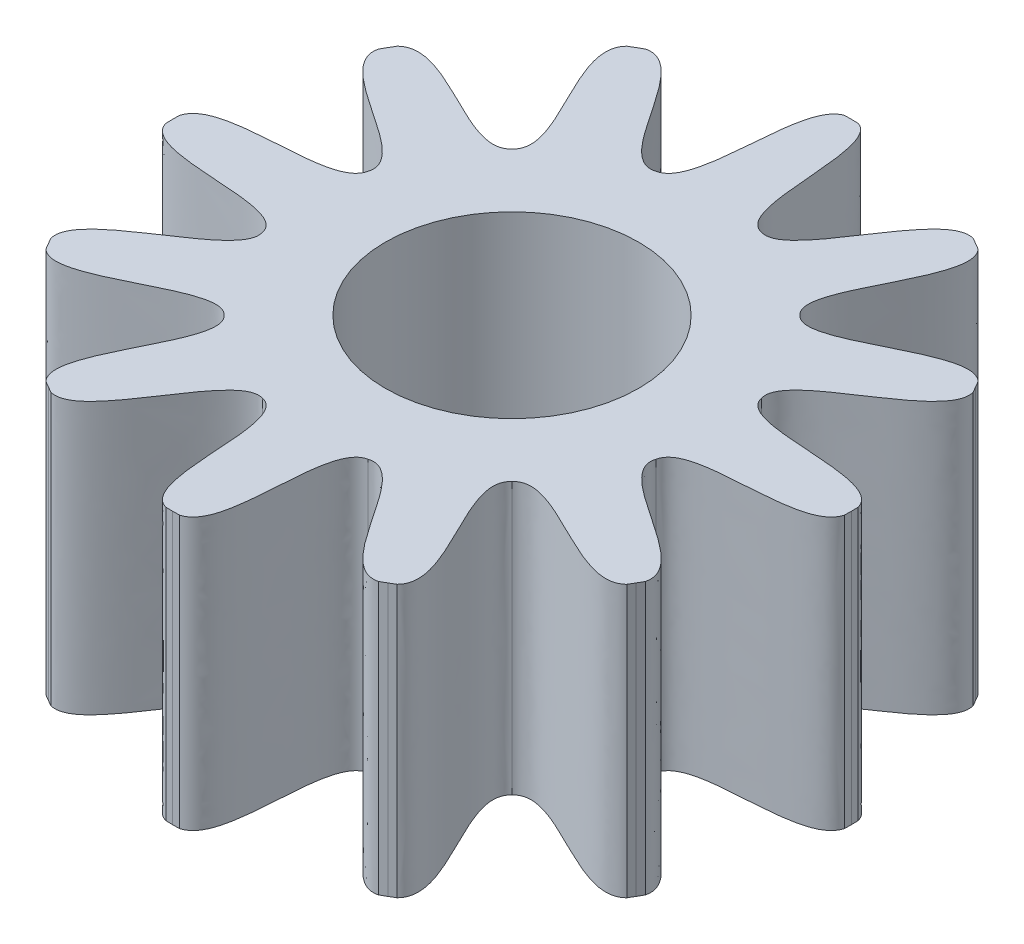
SolidWorks part; units mm, degrees
ref_plane "Alzado" through (0, 0, 0) normal (0, 0, 1) x (1, 0, 0)
ref_plane "Planta" through (0, 0, 0) normal (0, 1, 0) x (1, 0, 0)
ref_plane "Vista lateral" through (0, 0, 0) normal (1, 0, 0) x (0, 0, -1)
sketch "Sketch1" plane through (0, 0, 0) normal (0, 1, 0) x (1, 0, 0)
  line L0 (0, -1000) -> (0, 49000) construction
  line L1 (0, 0) -> (12940.9523, 48296.2913) construction
  line L2 (0, 0.75) -> (0.015, 0.7499)
  line L3 (0, 0.75) -> (-0.015, 0.7499)
  line L4 (0.375, 0.6495) -> (0.3619, 0.6569)
  line L5 (0.375, 0.6495) -> (0.3879, 0.6419)
  line L6 (0.6495, 0.375) -> (0.6419, 0.3879)
  line L7 (0.6495, 0.375) -> (0.6569, 0.3619)
  line L8 (0.75, 0) -> (0.7499, 0.015)
  line L9 (0.75, 0) -> (0.7499, -0.015)
  line L10 (0.6495, -0.375) -> (0.6569, -0.3619)
  line L11 (0.6495, -0.375) -> (0.6419, -0.3879)
  line L12 (0.375, -0.6495) -> (0.3879, -0.6419)
  line L13 (0.375, -0.6495) -> (0.3619, -0.6569)
  line L14 (0, -0.75) -> (0.015, -0.7499)
  line L15 (0, -0.75) -> (-0.015, -0.7499)
  line L16 (-0.375, -0.6495) -> (-0.3619, -0.6569)
  line L17 (-0.375, -0.6495) -> (-0.3879, -0.6419)
  line L18 (-0.6495, -0.375) -> (-0.6419, -0.3879)
  line L19 (-0.6495, -0.375) -> (-0.6569, -0.3619)
  line L20 (-0.75, 0) -> (-0.7499, -0.015)
  line L21 (-0.75, 0) -> (-0.7498, 0.015)
  line L22 (-0.6495, 0.375) -> (-0.6569, 0.3619)
  line L23 (-0.6495, 0.375) -> (-0.6419, 0.3879)
  line L24 (-0.375, 0.6495) -> (-0.3879, 0.6419)
  line L25 (-0.375, 0.6495) -> (-0.3619, 0.6569)
  circle A0 centre (0, 0) radius 0.75 construction
  circle A1 centre (0, 0) radius 0.45 construction
  spline S0 degree 3 poles (0.015, 0.7499) (0.0898, 0.7265) (0.0375, 0.4506) (0.1165, 0.4347) knots 0 0 0 0 1 1 1 1
  spline S1 degree 3 poles (-0.015, 0.7499) (-0.0898, 0.7265) (-0.0375, 0.4506) (-0.1165, 0.4347) knots 0 0 0 0 1 1 1 1
  spline S2 degree 3 poles (0.3619, 0.6569) (0.2767, 0.6794) (0.1928, 0.409) (0.1165, 0.4347) knots 0 0 0 0 1 1 1 1
  spline S3 degree 3 poles (0.3879, 0.6419) (0.4501, 0.5793) (0.2578, 0.3714) (0.3182, 0.3182) knots 0 0 0 0 1 1 1 1
  spline S4 degree 3 poles (0.6419, 0.3879) (0.5793, 0.4501) (0.3714, 0.2578) (0.3182, 0.3182) knots 0 0 0 0 1 1 1 1
  spline S5 degree 3 poles (0.6569, 0.3619) (0.6794, 0.2767) (0.409, 0.1928) (0.4347, 0.1165) knots 0 0 0 0 1 1 1 1
  spline S6 degree 3 poles (0.7499, 0.015) (0.7268, 0.1001) (0.4506, 0.0375) (0.4347, 0.1165) knots 0 0 0 0 1 1 1 1
  spline S7 degree 3 poles (0.7499, -0.015) (0.7268, -0.1001) (0.4506, -0.0375) (0.4347, -0.1165) knots 0 0 0 0 1 1 1 1
  spline S8 degree 3 poles (0.6569, -0.3619) (0.6794, -0.2767) (0.409, -0.1928) (0.4347, -0.1165) knots 0 0 0 0 1 1 1 1
  spline S9 degree 3 poles (0.6419, -0.3879) (0.5793, -0.4501) (0.3714, -0.2578) (0.3182, -0.3182) knots 0 0 0 0 1 1 1 1
  spline S10 degree 3 poles (0.3879, -0.6419) (0.4501, -0.5793) (0.2578, -0.3714) (0.3182, -0.3182) knots 0 0 0 0 1 1 1 1
  spline S11 degree 3 poles (0.3619, -0.6569) (0.2767, -0.6794) (0.1928, -0.409) (0.1165, -0.4347) knots 0 0 0 0 1 1 1 1
  spline S12 degree 3 poles (0.015, -0.7498) (0.1001, -0.7268) (0.0375, -0.4506) (0.1165, -0.4347) knots 0 0 0 0 1 1 1 1
  spline S13 degree 3 poles (-0.015, -0.7498) (-0.1001, -0.7268) (-0.0375, -0.4506) (-0.1165, -0.4347) knots 0 0 0 0 1 1 1 1
  spline S14 degree 3 poles (-0.3619, -0.6569) (-0.2767, -0.6794) (-0.1928, -0.409) (-0.1165, -0.4347) knots 0 0 0 0 1 1 1 1
  spline S15 degree 3 poles (-0.3879, -0.6419) (-0.4501, -0.5793) (-0.2578, -0.3714) (-0.3182, -0.3182) knots 0 0 0 0 1 1 1 1
  spline S16 degree 3 poles (-0.6419, -0.3879) (-0.5793, -0.4501) (-0.3714, -0.2578) (-0.3182, -0.3182) knots 0 0 0 0 1 1 1 1
  spline S17 degree 3 poles (-0.6569, -0.3619) (-0.6794, -0.2767) (-0.409, -0.1928) (-0.4347, -0.1165) knots 0 0 0 0 1 1 1 1
  spline S18 degree 3 poles (-0.7498, -0.015) (-0.7268, -0.1001) (-0.4506, -0.0375) (-0.4347, -0.1165) knots 0 0 0 0 1 1 1 1
  spline S19 degree 3 poles (-0.7498, 0.015) (-0.7268, 0.1001) (-0.4506, 0.0375) (-0.4347, 0.1165) knots 0 0 0 0 1 1 1 1
  spline S20 degree 3 poles (-0.6569, 0.3619) (-0.6794, 0.2767) (-0.409, 0.1928) (-0.4347, 0.1165) knots 0 0 0 0 1 1 1 1
  spline S21 degree 3 poles (-0.6419, 0.3879) (-0.5793, 0.4501) (-0.3714, 0.2578) (-0.3182, 0.3182) knots 0 0 0 0 1 1 1 1
  spline S22 degree 3 poles (-0.3879, 0.6419) (-0.4501, 0.5793) (-0.2578, 0.3714) (-0.3182, 0.3182) knots 0 0 0 0 1 1 1 1
  spline S23 degree 3 poles (-0.3619, 0.6569) (-0.2767, 0.6794) (-0.1928, 0.409) (-0.1165, 0.4347) knots 0 0 0 0 1 1 1 1
  point P4 (0.015, 0.7499)
  point P9 (0, 0.75)
  point P10 (0.1165, 0.4347)
  point P74 (0, 0)
  dimension "D1" = 1.5
  dimension "D2" = 0.9
  dimension "D3" = 15
  dimension "D4" = 0.015
  dimension "D5" = 12
extrude "Boss-Extrude1 (12 teeth)" add sketch "Sketch1" along normal blind 0.6
sketch "Sketch2" plane through (0, 0, 0) normal (0, 1, 0) x (1, 0, 0)
  circle A0 centre (0, 0) radius 0.28
  dimension "D1" = 0.56
extrude "Cut-Extrude1" cut sketch "Sketch2" along normal up to next
